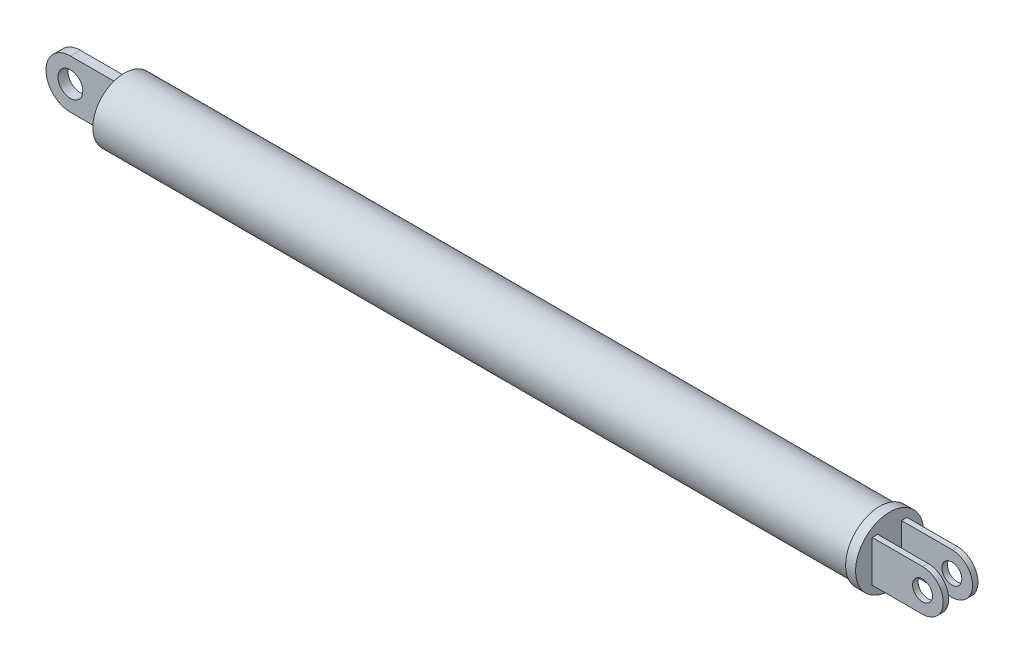
SolidWorks part; units mm, degrees
material "Cast Stainless Steel"
ref_plane "Front Plane" through (0, 0, 0) normal (0, 0, 1) x (1, 0, 0)
ref_plane "Top Plane" through (0, 0, 0) normal (0, 1, 0) x (1, 0, 0)
ref_plane "Right Plane" through (0, 0, 0) normal (1, 0, 0) x (0, 0, -1)
sketch "Sketch1" plane through (0, 0, 0) normal (1, 0, 0) x (0, 0, -1)
  circle A0 centre (0, 0) radius 12.7
  dimension "D1" = 25.4
extrude "Extrude1" add sketch "Sketch1" along normal blind 304
sketch "Sketch2" plane through (0, 0, 0) normal (0, 0, 1) x (1, 0, 0)
  line L0 (0, 0) -> (-32.8673, 0) construction
  line L1 (15.07, 0) -> (-15.07, 0) construction
  line L2 (0, 9.8057) -> (-19.7331, 9.8057)
  line L3 (0, 12.7) -> (0, -12.7) construction
  line L4 (0, -9.8057) -> (-19.7331, -9.8057)
  line L5 (0, 9.8057) -> (0, -9.8057)
  arc A0 (-19.7331, 9.8057) -> (-19.7331, -9.8057) centre (-19.7331, 0) ccw
  circle A1 centre (-19.7331, 0) radius 5
  dimension "D1" = 10
extrude "Extrude2" add sketch "Sketch2" along normal mid plane 4
sketch "Sketch3" plane through (304, 0, 0) normal (1, 0, 0) x (0, 0, -1)
  circle A2 centre (0, 0) radius 13.7
  circle A3 centre (0, 0) radius 13.7
  dimension "D1" = 1
extrude "Extrude3" add sketch "Sketch3" along normal blind 4
sketch "Sketch4" plane through (0, 0, 0) normal (0, 0, 1) x (1, 0, 0)
  line L0 (308, 8.3247) -> (328.2389, 8.3247)
  line L1 (308, -13.7) -> (308, 13.7) construction
  line L2 (331.2897, 0) -> (364.956, 0) construction
  line L3 (308, -8.3247) -> (328.2389, -8.3247)
  line L4 (308, 8.3247) -> (308, -8.3247)
  arc A0 (328.2389, 8.3247) -> (328.2389, -8.3247) centre (328.2389, 0) cw
  circle A1 centre (328.2389, 0) radius 4
  dimension "D1" = 8
extrude "Extrude4" add sketch "Sketch4" along normal mid plane 14
sketch "Sketch5" plane through (0, 0, 0) normal (0, 1, 0) x (1, 0, 0)
  line L0 (302.6802, 0) -> (363.3519, 0) construction
  line L1 (-15.07, 0) -> (15.07, 0) construction
  line L2 (308, -13.7) -> (308, 13.7) construction
  line L3 (308, 4.8012) -> (359.728, 4.8012)
  line L4 (308, 4.8012) -> (308, -4.8012)
  line L5 (308, -4.8012) -> (359.728, -4.8012)
  line L6 (359.728, 4.8012) -> (359.728, -4.8012)
  line L7 (359.728, 0) -> (308, 0) construction
extrude "Cut-Extrude1" cut sketch "Sketch5" against normal through all and the other way through all
